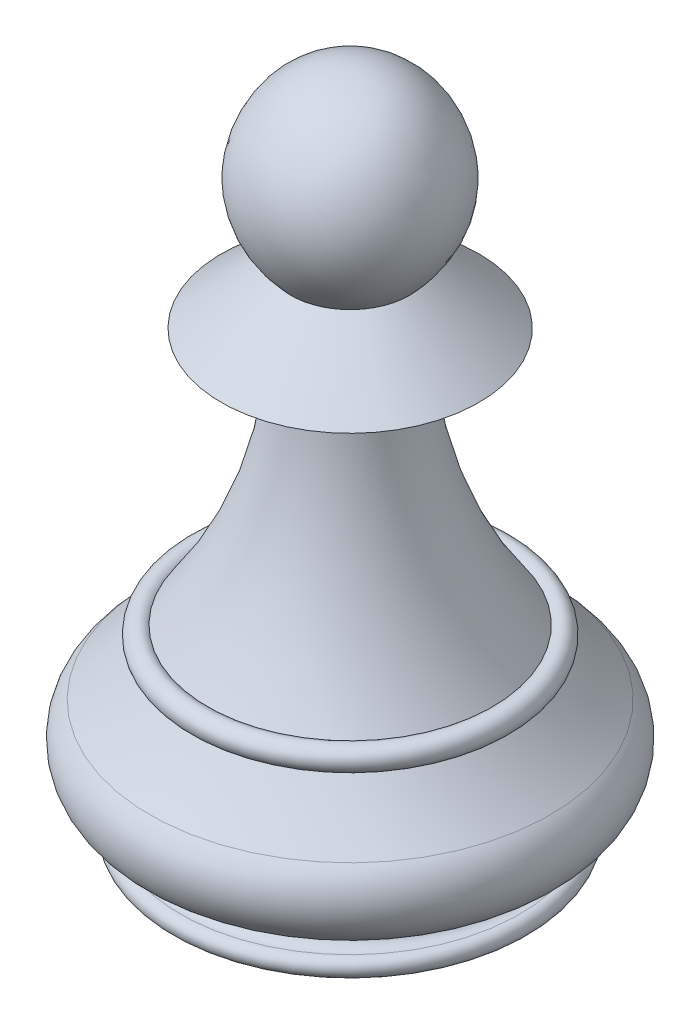
SolidWorks part; units mm, degrees
material "Maple"
ref_plane "Front Plane" through (0, 0, 0) normal (0, 0, 1) x (1, 0, 0)
ref_plane "Top Plane" through (0, 0, 0) normal (0, 1, 0) x (1, 0, 0)
ref_plane "Right Plane" through (0, 0, 0) normal (1, 0, 0) x (0, 0, -1)
sketch "Sketch2" plane through (0, 0, 0) normal (0, 0, 1) x (1, 0, 0)
  line L0 (0, 0) -> (0, 29.42)
  line L1 (0, 0) -> (7.5, 0)
  line L2 (2.5872, 19.4934) -> (5.6972, 19.4934)
  line L3 (5.6972, 19.4934) -> (2.62, 22.0534)
  line L4 (4.01, 23.8609) -> (4.01, 26.3521) construction
  arc A0 (7.5, 0) -> (7.5, 0.8) centre (7.5, 0.4) ccw
  arc A1 (7.5, 0.8) -> (7.5, 1.8) centre (7.5, 1.3) cw
  arc A2 (7.5, 1.8) -> (8.85, 5.2756) centre (7.5, 3.8) ccw
  arc A3 (8.85, 5.2756) -> (6.9, 7.3438) centre (21.8572, 19.4934) cw
  arc A4 (6.2915, 8.1338) -> (6.9, 7.3438) centre (6.6256, 7.7617) cw
  arc A5 (6.2915, 8.1338) -> (2.5872, 19.4934) centre (21.8572, 19.4934) cw
  spline S0 degree 3 poles (0, 29.42) (2.4533, 29.42) (4.9803, 25.4983) (3.4327, 22.9097) (2.62, 22.0534) knots 0 0 0 0 0.512538 1 1 1 1
  dimension "D3" = 0.4
  dimension "D4" = 0.5
  dimension "D5" = 2
  dimension "D7" = 19.27
  dimension "D13" = 0.5
  dimension "D1" = 29.42
  dimension "D2" = 7.5
  dimension "D6" = 8.85
  dimension "D8" = 3.11
  dimension "D9" = 2.56
  dimension "D10" = 2.62
  dimension "D11" = 25.21
  dimension "D12" = 4.01
  dimension "D14" = 0.79
  dimension "D15" = 6.9
revolve "Revolve1" add sketch "Sketch2" angle 360 about L0
